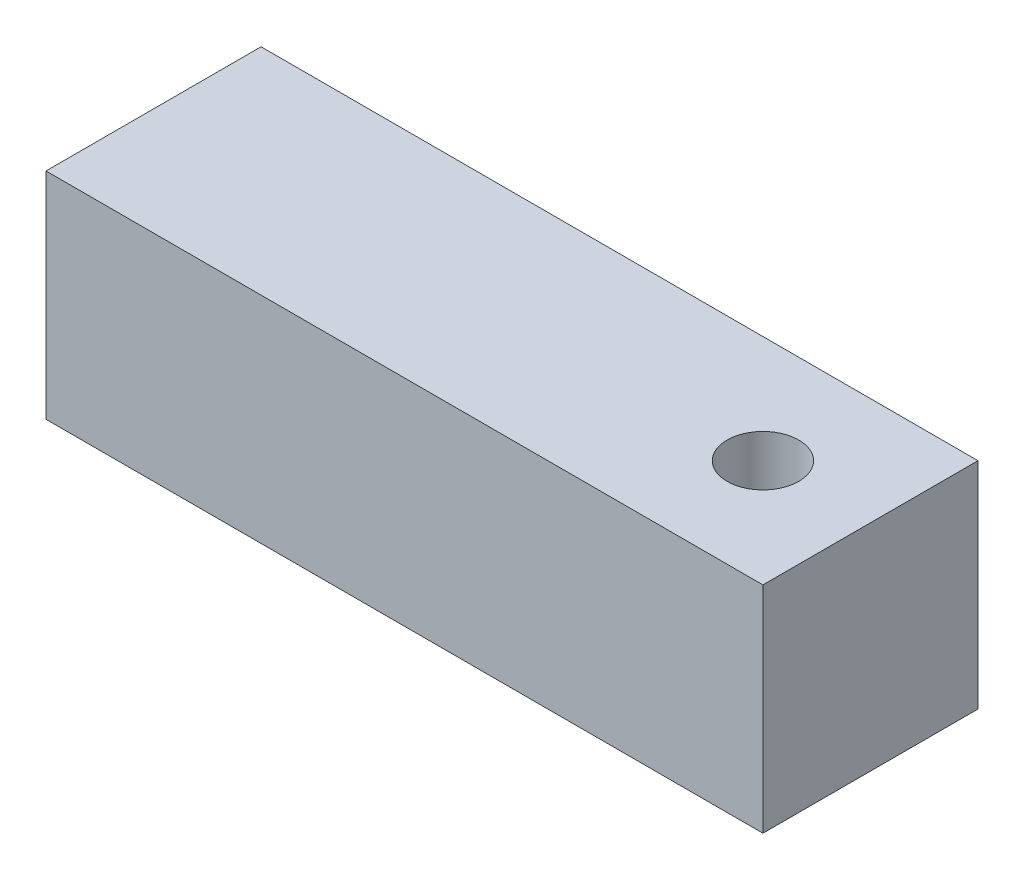
SolidWorks part; units mm, degrees
ref_plane "Front Plane" through (0, 0, 0) normal (0, 0, 1) x (1, 0, 0)
ref_plane "Top Plane" through (0, 0, 0) normal (0, 1, 0) x (1, 0, 0)
ref_plane "Right Plane" through (0, 0, 0) normal (1, 0, 0) x (0, 0, -1)
sketch "Sketch1" plane through (0, 0, 0) normal (0, 1, 0) x (1, 0, 0)
  line L0 (0, 7.5) -> (42.5, 7.5) construction
  line L1 (0, 0) -> (50, 0)
  line L2 (0, 0) -> (0, 15)
  line L3 (0, 15) -> (50, 15)
  line L4 (50, 0) -> (50, 15)
  circle A0 centre (42.5, 7.5) radius 2.5
  point P8 (40, 7.5)
  dimension "D3" = 5
  dimension "D1" = 42.5
  dimension "D2" = 15
  dimension "D4" = 50
extrude "Boss-Extrude1" add sketch "Sketch1" along normal blind 15
